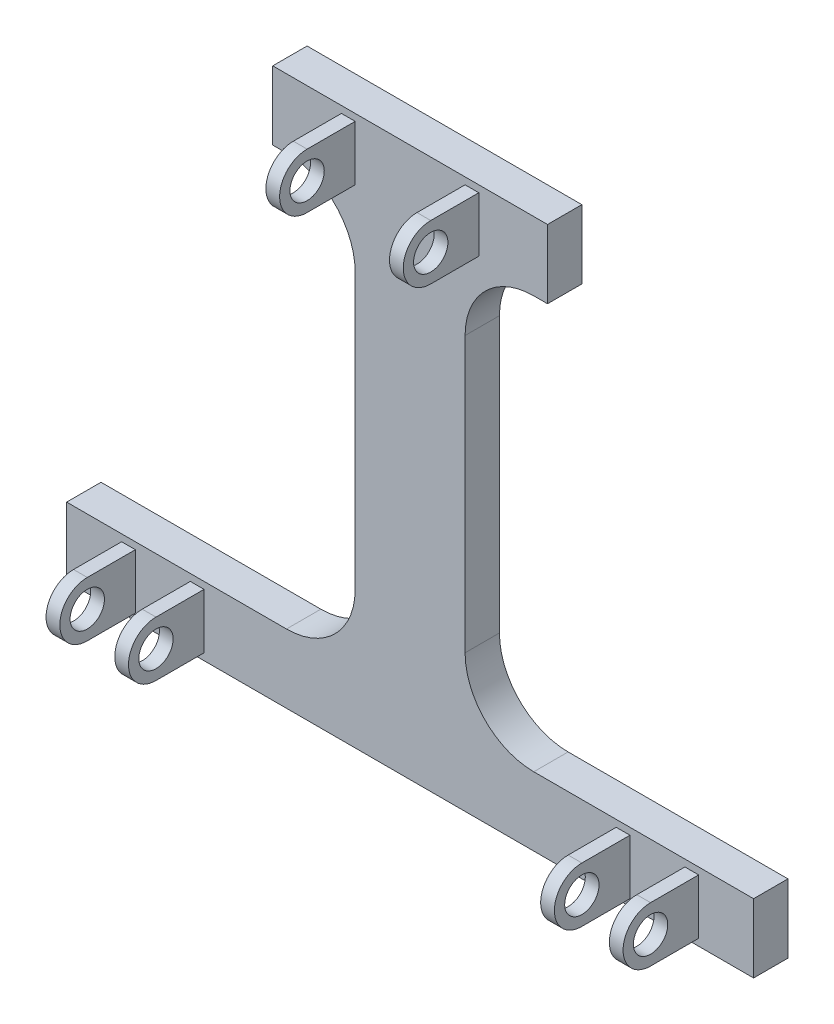
SolidWorks part; units mm, degrees
ref_plane "Front Plane" through (0, 0, 0) normal (0, 0, 1) x (1, 0, 0)
ref_plane "Top Plane" through (0, 0, 0) normal (0, 1, 0) x (1, 0, 0)
ref_plane "Right Plane" through (0, 0, 0) normal (1, 0, 0) x (0, 0, -1)
sketch "Sketch2" plane through (0, 0, 0) normal (0, 0, 1) x (1, 0, 0)
  line L0 (0, 0) -> (0, 80) construction
  line L1 (-20, 80) -> (20, 80)
  line L2 (50, 10) -> (18, 10)
  line L3 (50, 0) -> (-50, 0)
  line L4 (-20, 70) -> (-18, 70)
  line L5 (-20, 70) -> (-20, 80)
  line L6 (20, 80) -> (20, 70)
  line L7 (50, 10) -> (50, 0)
  line L8 (-50, 0) -> (-50, 10)
  line L9 (-8, 60) -> (-8, 20)
  line L10 (8, 60) -> (8, 20)
  line L11 (-20, 70) -> (20, 70) construction
  line L12 (-18, 10) -> (-50, 10)
  line L13 (50, 10) -> (-50, 10) construction
  line L14 (20, 70) -> (18, 70)
  arc A0 (8, 20) -> (18, 10) centre (18, 20) ccw
  arc A1 (-8, 20) -> (-18, 10) centre (-18, 20) cw
  arc A2 (8, 60) -> (18, 70) centre (18, 60) cw
  arc A3 (-8, 60) -> (-18, 70) centre (-18, 60) ccw
  point P17 (8, 10)
  point P20 (-8, 10)
  point P23 (8, 70)
  point P26 (-8, 70)
  dimension "D6" = 10
  dimension "D1" = 40
  dimension "D2" = 100
  dimension "D3" = 80
  dimension "D5" = 8
  dimension "D4" = 10
extrude "Boss-Extrude1" add sketch "Sketch2" along normal blind 5
sketch "Sketch4" plane through (0, 0, 5) normal (0, 0, 1) x (1, 0, 0)
  line L0 (0, 80) -> (0, 0) construction
  line L1 (20, 80) -> (-20, 80) construction
  line L2 (-20, 75) -> (-10, 75) construction
  line L3 (-20, 80) -> (-20, 70) construction
  line L4 (-10, 79) -> (-10, 71)
  line L5 (-8, 79) -> (-8, 71)
  line L6 (-10, 79) -> (-8, 79)
  line L7 (-8, 71) -> (-10, 71)
  line L8 (10, 79) -> (8, 79)
  line L9 (8, 79) -> (8, 71)
  line L10 (8, 71) -> (10, 71)
  line L11 (10, 79) -> (10, 71)
  line L12 (-50, 5) -> (-42, 5) construction
  line L13 (-50, 10) -> (-50, 0) construction
  line L14 (-42, 9) -> (-42, 1)
  line L15 (-42, 9) -> (-40, 9)
  line L16 (-40, 9) -> (-40, 1)
  line L17 (-40, 1) -> (-42, 1)
  line L18 (-40, 5) -> (-32, 5) construction
  line L19 (-32, 9) -> (-32, 1)
  line L20 (-32, 1) -> (-30, 1)
  line L21 (-30, 1) -> (-30, 9)
  line L22 (-30, 9) -> (-32, 9)
  line L23 (30, 9) -> (32, 9)
  line L24 (30, 1) -> (30, 9)
  line L25 (32, 1) -> (30, 1)
  line L26 (32, 9) -> (32, 1)
  line L27 (42, 9) -> (42, 1)
  line L28 (40, 1) -> (42, 1)
  line L29 (40, 9) -> (40, 1)
  line L30 (42, 9) -> (40, 9)
  dimension "D1" = 8
  dimension "D2" = 8
  dimension "D4" = 8
  dimension "D5" = 30
  dimension "D3" = 2
extrude "Boss-Extrude2" add sketch "Sketch4" along normal blind 12
sketch "Sketch5" plane through (0, 0, 0) normal (1, 0, 0) x (0, 0, -1)
  line L0 (-17, 5) -> (-12, 5) construction
  line L1 (-17, 1) -> (-17, 9) construction
  line L2 (-12, 75) -> (-17, 75) construction
  line L3 (-17, 71) -> (-17, 79) construction
  line L4 (-17, 79) -> (-5, 79) construction
  line L5 (-17, 71) -> (-5, 71) construction
  line L6 (-12, 79) -> (-17, 79)
  line L7 (-17, 79) -> (-17, 71)
  line L8 (-17, 71) -> (-12, 71)
  line L9 (-17, 9) -> (-5, 9) construction
  line L10 (-17, 1) -> (-5, 1) construction
  line L11 (-12, 9) -> (-17, 9)
  line L12 (-17, 9) -> (-17, 1)
  line L13 (-17, 1) -> (-12, 1)
  circle A0 centre (-12, 75) radius 2.5
  circle A1 centre (-12, 5) radius 2.5
  arc A2 (-12, 79) -> (-12, 71) centre (-12, 75) ccw
  arc A3 (-12, 9) -> (-12, 1) centre (-12, 5) ccw
  dimension "D1" = 5
  dimension "D2" = 5
extrude "Cut-Extrude1" cut sketch "Sketch5" against normal through all and the other way through all
